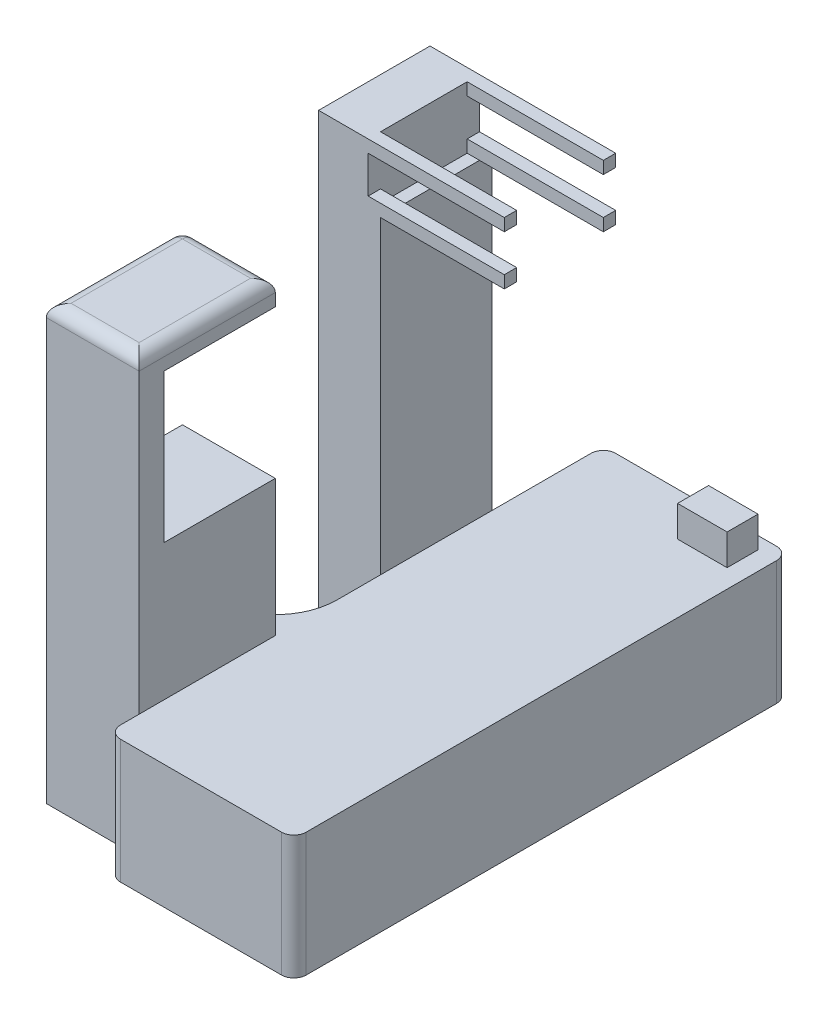
SolidWorks part; units mm, degrees
ref_plane "Front Plane" through (0, 0, 0) normal (0, 0, 1) x (1, 0, 0)
ref_plane "Top Plane" through (0, 0, 0) normal (0, 1, 0) x (1, 0, 0)
ref_plane "Right Plane" through (0, 0, 0) normal (1, 0, 0) x (0, 0, -1)
sketch "Sketch5" plane through (0, 0, 0) normal (0, 1, 0) x (1, 0, 0)
  line L1 (15, 40) -> (-15, 40)
  line L2 (15, 40) -> (15, -40)
  line L3 (15, -40) -> (-15, -40)
  line L4 (-15, 40) -> (-15, -40)
  line L5 (15, 40) -> (-15, -40) construction
  line L6 (15, -40) -> (-15, 40) construction
  point P0 (0, 0)
  dimension "D1" = 80
  dimension "D2" = 30
extrude "Boss-Extrude4" add sketch "Sketch5" along normal blind 20
sketch "Sketch6" plane through (0, 20, 0) normal (0, 1, 0) x (1, 0, 0)
  line L0 (15, 40) -> (-15, 40) construction
  line L1 (12, 38) -> (4, 38)
  line L2 (12, 38) -> (12, 33)
  line L3 (12, 33) -> (4, 33)
  line L4 (4, 38) -> (4, 33)
  line L5 (12, 38) -> (4, 33) construction
  line L6 (12, 33) -> (4, 38) construction
  line L9 (0, 0) -> (0, 40) construction
  line L10 (-15, 40) -> (-15, -40) construction
  point P0 (8, 35.5)
  dimension "D1" = 8
  dimension "D2" = 5
  dimension "D3" = 2
  dimension "D4" = 19
extrude "Boss-Extrude5" add sketch "Sketch6" along normal blind 5 contours L3 L4 L1 L2
sketch "Sketch9" plane through (0, 0, 0) normal (0, 1, 0) x (1, 0, 0)
  line L0 (-15, 40) -> (-15, -40) construction
  line L5 (-15, -35) -> (-30, -35)
  line L6 (-15, -35) -> (-15, -13)
  line L7 (-15, -13) -> (-30, -13)
  line L8 (-30, -35) -> (-30, -13)
  line L9 (-15, -40) -> (15, -40) construction
  point P13 (-22.5, -13)
  dimension "D4" = 5
  dimension "D5" = 22
  dimension "D6" = 7.5
sketch "Sketch13" plane through (0, 20, 0) normal (0, 1, 0) x (1, 0, 0)
  line L0 (-15, 40) -> (-15, -40) construction
  line L2 (-15, -40) -> (15, -40) construction
  circle A0 centre (-10.8598, -10) radius 3
  circle A1 centre (40.5752, -10) radius 3
  circle A2 centre (14.845, -25.24) radius 3
  dimension "D1" = 4.1402
  dimension "D3" = 6
  dimension "D4" = 51.435
  dimension "D6" = 6
  dimension "D7" = 6
  dimension "D2" = 30
  dimension "D5" = 25.7302
  dimension "D8" = 25.7048
  dimension "D9" = 15.24
extrude "Boss-Extrude8" [suppressed] add sketch "Sketch13" along normal blind 20
extrude "Boss-Extrude10" add sketch "Sketch9" along normal blind 70 contours L8 L7 L6 L5
sketch "Sketch14" plane through (0, 0, 13) normal (0, 0, -1) x (-1, 0, 0)
  line L0 (15, 70) -> (15, 20) construction
  line L1 (15, 42) -> (30, 42)
  line L2 (15, 42) -> (15, 66)
  line L3 (15, 66) -> (30, 66)
  line L4 (30, 42) -> (30, 66)
  line L5 (30, 70) -> (30, 0) construction
  line L7 (15, 0) -> (30, 0) construction
  dimension "D1" = 42
  dimension "D2" = 24
extrude "Cut-Extrude1" cut sketch "Sketch14" against normal blind 18 contours L3 L4 L1 L2
fillet "Fillet1" radius 2 4 edges at (-15, 10, -40) (15, 10, -40) (-15, 10, 40) (15, 10, 40)
fillet "Fillet2" radius 10 1 edges at (-15, 10, 13)
fillet "Fillet4" radius 2 1 edges at (-30, 68, 13)
fillet "Fillet6" radius 2 5 edges at (-15, 70, 24) (-22.5, 70, 35) (-30, 70, 25) (-29.4142, 70, 13.5858) (-21.5, 70, 13)
sketch "Sketch15" [suppressed] plane through (0, 40, 0) normal (0, 1, 0) x (1, 0, 0)
  circle A0 centre (23.8252, -10) radius 1.6383
  circle A1 centre (23.8252, -10) radius 3 construction
  circle A2 centre (-1.905, -25.24) radius 2
  circle A3 centre (-1.905, -25.24) radius 3 construction
  circle A5 centre (-27.6098, -10) radius 2.5
  dimension "D1" = 3.2766
  dimension "D3" = 4
  dimension "D4" = 5
  dimension "D2" = 0
  dimension "D5" = 0
extrude "Cut-Extrude2" [suppressed] cut sketch "Sketch15" against normal blind 1 draft 8
sketch "Sketch16" [suppressed] plane through (0, 39, 0) normal (0, 1, 0) x (1, 0, 0)
  circle A0 centre (23.8252, -10) radius 1.4986
  circle A1 centre (23.8252, -10) radius 3 construction
  circle A2 centre (-1.905, -25.24) radius 2
  circle A3 centre (-27.6098, -10) radius 2.5
  circle A5 centre (-1.905, -25.24) radius 3 construction
  dimension "D1" = 2.9972
  dimension "D3" = 4
  dimension "D4" = 5
  dimension "D2" = 0
  dimension "D6" = 0
extrude "Cut-Extrude3" [suppressed] cut sketch "Sketch16" against normal blind 7
sketch "Sketch18" plane through (0, 0, 0) normal (0, -1, 0) x (-1, 0, 0)
  line L0 (25, -13) -> (30, -13) construction
  line L1 (15, 22) -> (25, 22)
  line L2 (15, 22) -> (15, 4)
  line L3 (15, 4) -> (25, 4)
  line L4 (25, 22) -> (25, 4)
  line L5 (15, 38) -> (15, -3) construction
  dimension "D1" = 17
  dimension "D3" = 18
  dimension "D4" = 10
extrude "Boss-Extrude11" add sketch "Sketch18" against normal blind 80 contours L1 L4 L3 L2
sketch "Sketch19" plane through (0, 80, 0) normal (0, 1, 0) x (1, 0, 0)
  line L1 (-15, 22) -> (5, 22)
  line L2 (-15, 22) -> (-15, 14.7413)
  line L3 (-15, 6.7413) -> (-15, 14.7413)
  line L4 (5, 22) -> (5, 14.7413)
  line L5 (-15, 4) -> (5, 4)
  line L6 (-15, 4) -> (-15, 6.7413)
  line L8 (5, 4) -> (5, 6.7413)
  line L9 (5, 6.7413) -> (5, 14.7413)
  dimension "D3" = 20
extrude "Boss-Extrude12" add sketch "Sketch19" against normal blind 10
sketch "Sketch20" plane through (5, 0, 0) normal (1, 0, 0) x (0, 0, -1)
  line L0 (4, 80) -> (22, 80) construction
  line L1 (20, 80) -> (6, 80)
  line L2 (20, 80) -> (20, 78)
  line L3 (20, 70) -> (6, 70)
  line L4 (6, 80) -> (6, 78)
  line L5 (4, 70) -> (22, 70) construction
  line L7 (4, 72) -> (6, 72)
  line L8 (4, 72) -> (4, 78)
  line L9 (4, 78) -> (6, 78)
  line L10 (22, 72) -> (22, 78)
  line L11 (22, 70) -> (22, 80) construction
  line L12 (4, 70) -> (4, 80) construction
  line L13 (6, 72) -> (6, 70)
  line L14 (20, 78) -> (22, 78)
  line L15 (20, 72) -> (20, 70)
  line L16 (20, 72) -> (22, 72)
  point P8 (13, 80)
  dimension "D1" = 7
  dimension "D2" = 2
  dimension "D3" = 2
  dimension "D4" = 0
  dimension "D5" = 2
extrude "Cut-Extrude4" cut sketch "Sketch20" against normal blind 22 contours L9 L4 L1 L2 L14 L10 L16 L15 L3 L13 L7 L8
